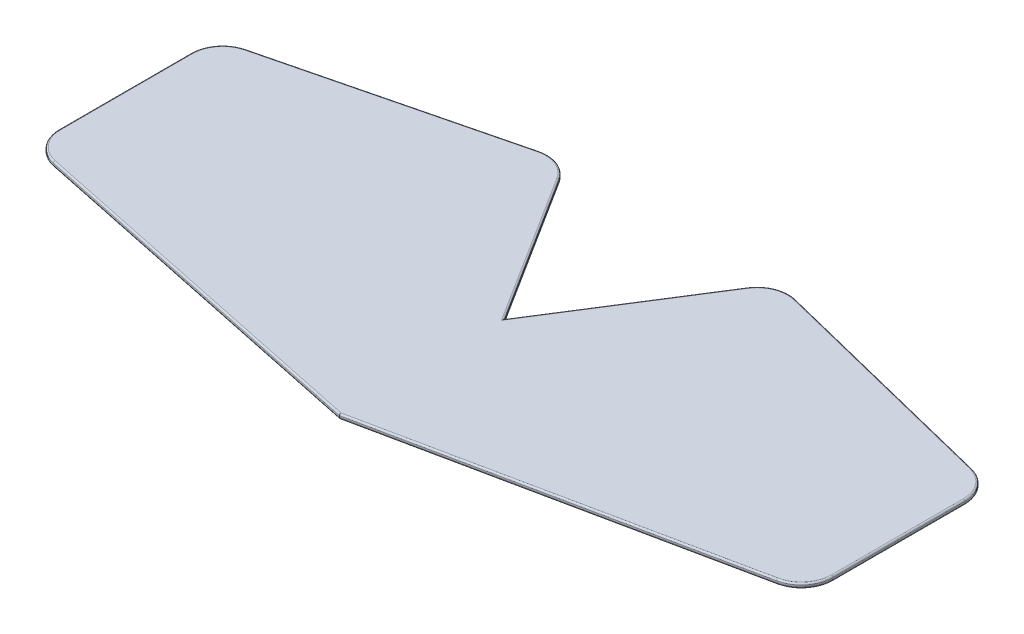
SolidWorks part; units mm, degrees
ref_plane "Front Plane" through (0, 0, 0) normal (0, 0, 1) x (1, 0, 0)
ref_plane "Top Plane" through (0, 0, 0) normal (0, 1, 0) x (1, 0, 0)
ref_plane "Right Plane" through (0, 0, 0) normal (1, 0, 0) x (0, 0, -1)
sketch "Sketch2" plane through (0, 0, 0) normal (0, 1, 0) x (1, 0, 0)
  line L0 (-1294.3835, -2900.7866) -> (-140.3835, -2900.7866) construction
sketch "Sketch1" plane through (0, 0, 0) normal (0, 1, 0) x (1, 0, 0)
  line L0 (0, 0) -> (-296.4201, 468.9632)
  line L1 (-405.0746, 512.5803) -> (-1144.1245, 328.8617)
  line L2 (-1220, 231.8153) -> (-1220, -183.7406)
  line L3 (-1140.4595, -281.6253) -> (0, -520)
  line L4 (0, -520) -> (1140.4595, -281.6253)
  line L7 (296.4201, 468.9632) -> (0, 0)
  line L8 (1220, -183.7406) -> (1220, 231.8153)
  line L9 (1144.1245, 328.8617) -> (405.0746, 512.5803)
  arc A0 (296.4201, 468.9632) -> (405.0746, 512.5803) centre (380.9501, 415.5339) cw
  arc A1 (-296.4201, 468.9632) -> (-405.0746, 512.5803) centre (-380.9501, 415.5339) ccw
  arc A2 (1140.4595, -281.6253) -> (1220, -183.7406) centre (1120, -183.7406) ccw
  arc A3 (1220, 231.8153) -> (1144.1245, 328.8617) centre (1120, 231.8153) ccw
  arc A4 (-1220, 231.8153) -> (-1144.1245, 328.8617) centre (-1120, 231.8153) cw
  arc A5 (-1220, -183.7406) -> (-1140.4595, -281.6253) centre (-1120, -183.7406) ccw
  point P20 (335, 530)
  point P23 (-335, 530)
  point P26 (1220, -265)
  point P29 (1220, 310)
  point P32 (-1220, 310)
  point P35 (-1220, -265)
  dimension "D13" = 100
  dimension "D1" = 2440
  dimension "D2" = 1220
  dimension "D3" = 255
  dimension "D4" = 255
  dimension "D5" = 575
  dimension "D6" = 575
  dimension "D7" = 520
  dimension "D8" = 530
  dimension "D9" = 530
  dimension "D10" = 335
  dimension "D11" = 335
  dimension "D12" = 220
extrude "Boss-Extrude1" add sketch "Sketch1" along normal blind 15
fillet "Fillet1" radius 5 28 edges at (-1220, 0, -24.0373) (-1198.7796, 0, -293.4089) (-774.5996, 0, -420.721) (-343.6967, 0, -508.3358) (-148.2101, 0, -234.4816) (343.6967, 0, -508.3358) (148.2101, 0, -234.4816) (774.5996, 0, -420.721) (1198.7796, 0, -293.4089) (1220, 0, -24.0373) (1197.6078, 0, 246.8043) (570.2298, 0, 400.8126) (-570.2298, 0, 400.8126) (-1197.6078, 0, 246.8043) (570.2298, 15, 400.8126) (1197.6078, 15, 246.8043) (1220, 15, -24.0373) (1198.7796, 15, -293.4089) (774.5996, 15, -420.721) (343.6967, 15, -508.3358) (148.2101, 15, -234.4816) (-343.6967, 15, -508.3358) (-148.2101, 15, -234.4816) (-774.5996, 15, -420.721) (-1198.7796, 15, -293.4089) (-1220, 15, -24.0373) (-1197.6078, 15, 246.8043) (-570.2298, 15, 400.8126)
